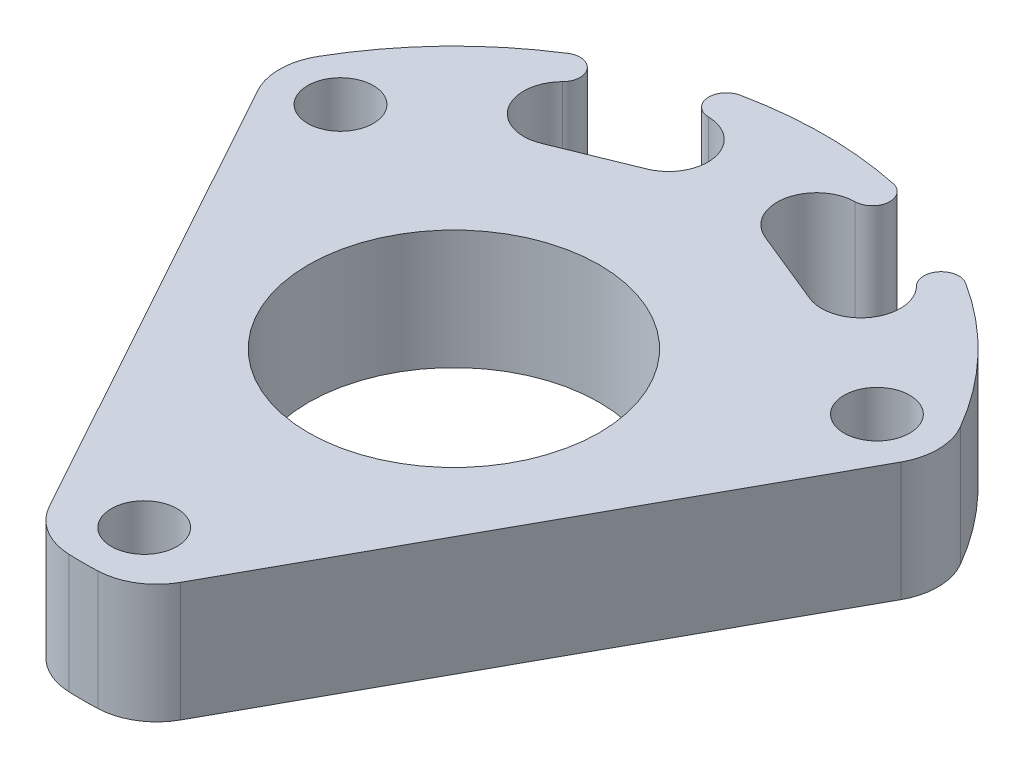
SolidWorks part; units mm, degrees
material "Cedar"
ref_plane "Front Plane" through (0, 0, 0) normal (0, 0, 1) x (1, 0, 0)
ref_plane "Top Plane" through (0, 0, 0) normal (0, 1, 0) x (1, 0, 0)
ref_plane "Right Plane" through (0, 0, 0) normal (1, 0, 0) x (0, 0, -1)
sketch "Sketch1" plane through (0, 0, 0) normal (0, 1, 0) x (1, 0, 0)
  line L0 (0, 16.5) -> (-14.2894, 8.25) construction
  line L1 (-14.2894, 8.25) -> (-14.2894, -8.25) construction
  line L2 (-17.1356, 6.6811) -> (-3.5, -18.056)
  line L3 (3.5, -18.056) -> (17.1356, 6.6811)
  arc A0 (-0.7825, -19.7345) -> (0.7825, -19.7345) centre (0, 0) ccw
  circle A1 centre (0, 0) radius 16.5 construction
  circle A2 centre (0, 0) radius 7.75
  circle A3 centre (0, 16.5) radius 1.75 construction
  circle A4 centre (-14.2894, 8.25) radius 1.75
  circle A5 centre (-14.2894, -8.25) radius 1.75 construction
  circle A6 centre (0, -16.5) radius 1.75
  circle A7 centre (14.2894, -8.25) radius 1.75 construction
  circle A8 centre (14.2894, 8.25) radius 1.75
  arc A9 (-17.104, 9.875) -> (-17.1356, 6.6811) centre (-14.2894, 8.25) ccw
  arc A10 (17.1356, 6.6811) -> (17.104, 9.875) centre (14.2894, 8.25) ccw
  arc A11 (17.104, 9.875) -> (-17.104, 9.875) centre (0, 0) ccw
  arc A12 (-0.7825, -19.7345) -> (-3.5, -18.056) centre (-0.6538, -16.487) cw
  arc A13 (3.5, -18.056) -> (0.7825, -19.7345) centre (0.6538, -16.487) cw
  dimension "D1" = 39.5
  dimension "D2" = 33
  dimension "D3" = 15.5
  dimension "D4" = 3.5
  dimension "D5" = 7
extrude "Boss-Extrude1" add sketch "Sketch1" along normal blind 6.35
sketch "Sketch2" plane through (0, 6.35, 0) normal (0, 1, 0) x (1, 0, 0)
  line L0 (0, 0) -> (0, 15.7203) construction
  line L1 (7.9375, 13.7482) -> (0, 0) construction
  line L2 (0, 0) -> (3.7596, 6.5118) construction
  line L3 (3.9391, 15.3785) -> (0, 0) construction
  line L4 (3.1479, 13.4381) -> (7.1463, 11.8078)
  arc A0 (7.1463, 11.8078) -> (9.4265, 15.2226) centre (7.9375, 13.7482) ccw
  circle A1 centre (0, 0) radius 19.75 construction
  arc A2 (10.5922, 16.6694) -> (4.084, 19.3231) centre (0, 0) ccw
  arc A3 (10.5922, 16.6694) -> (9.4265, 15.2226) centre (10.0908, 15.8804) ccw
  arc A5 (3.9057, 17.4738) -> (3.1479, 13.4381) centre (3.9391, 15.3785) ccw
  arc A6 (3.9057, 17.4738) -> (4.084, 19.3231) centre (3.8907, 18.4085) ccw
  arc A7 (-0.7825, -19.7345) -> (0.7825, -19.7345) centre (0, 0) ccw construction
  dimension "D2" = 4.191
  dimension "D3" = 4.826
  dimension "D1" = 15.875
  dimension "D4" = 4.318
  dimension "D6" = 30
extrude "Cut-Extrude1" cut sketch "Sketch2" against normal through all
mirror "Mirror1" about plane through (0, 0, 0) normal (1, 0, 0) of "Cut-Extrude1"
